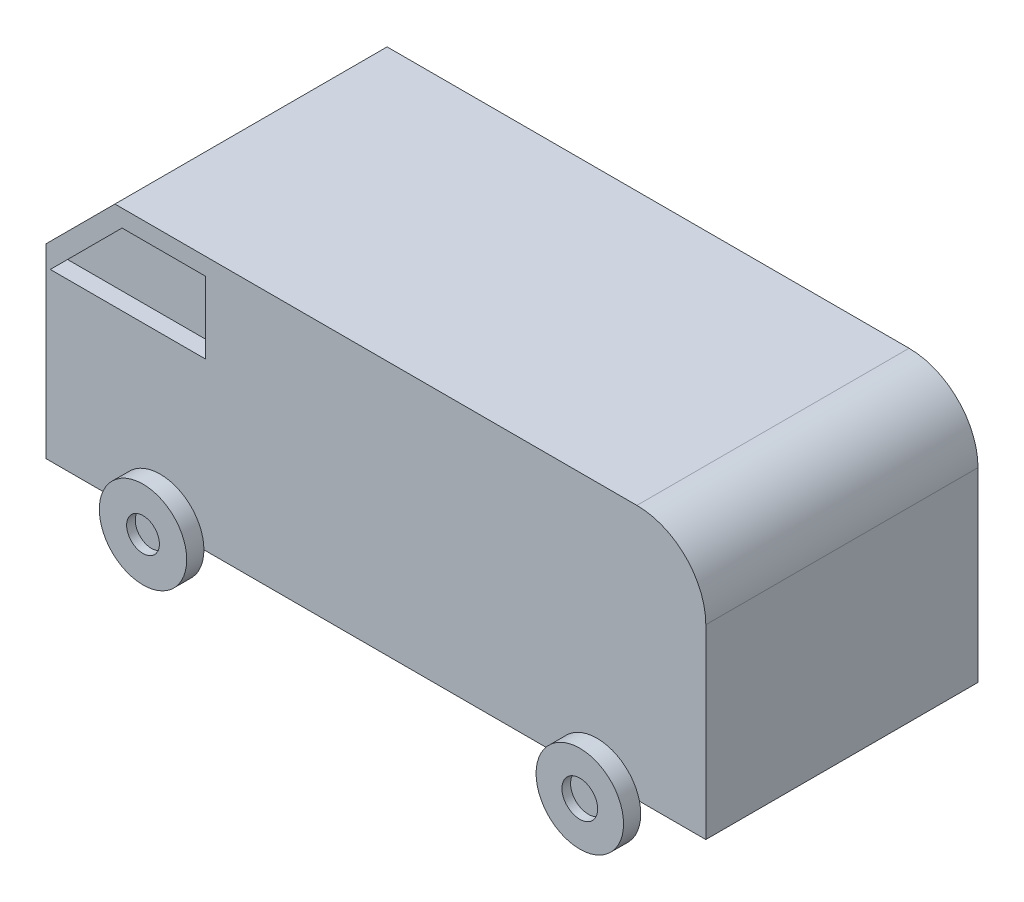
SolidWorks part; units mm, degrees
ref_plane "Front Plane" through (0, 0, 0) normal (0, 0, 1) x (1, 0, 0)
ref_plane "Top Plane" through (0, 0, 0) normal (0, 1, 0) x (1, 0, 0)
ref_plane "Right Plane" through (0, 0, 0) normal (1, 0, 0) x (0, 0, -1)
sketch "Sketch1" plane through (0, 0, 0) normal (0, 1, 0) x (1, 0, 0)
  line L1 (-191.5, -79) -> (191.5, -79)
  line L2 (-191.5, -79) -> (-191.5, 79)
  line L3 (-191.5, 79) -> (191.5, 79)
  line L4 (191.5, -79) -> (191.5, 79)
  line L5 (-191.5, -79) -> (191.5, 79) construction
  line L6 (-191.5, 79) -> (191.5, -79) construction
  point P0 (0, 0)
  dimension "D1" = 383
  dimension "D2" = 158
extrude "Boss-Extrude1" add sketch "Sketch1" along normal blind 148
chamfer "Chamfer1" distance 40 1 edges at (-191.5, 148, 0)
fillet "Fillet2" radius 40 1 edges at (191.5, 148, 0)
sketch "Sketch2" plane through (0, 0, 79) normal (0, 0, 1) x (1, 0, 0)
  line L5 (-147.3579, 138) -> (-188.9979, 96.36)
  line L6 (-188.9979, 96.36) -> (-98.9979, 96.36)
  line L7 (-98.9979, 96.36) -> (-98.9979, 138)
  line L8 (-98.9979, 138) -> (-147.3579, 138)
  line L9 (-151.5, 148) -> (151.5, 148) construction
  line L10 (-151.5, 148) -> (-191.5, 108) construction
  line L11 (-98.9979, 138) -> (-98.9979, 96.36)
  line L12 (-188.9979, 96.36) -> (-147.3579, 138)
  line L13 (-98.9979, 138) -> (-147.3579, 138)
  line L14 (-188.9979, 96.36) -> (-98.9979, 96.36)
  line L15 (-98.9979, 96.36) -> (-98.9979, 138)
  dimension "D1" = 90
  dimension "D2" = 41.64
  dimension "D3" = 10
  dimension "D4" = 10
extrude "Cut-Extrude1" cut sketch "Sketch2" against normal blind 10 contours L7 L8 L5 L6
sketch "Sketch3" plane through (0, 0, 79) normal (0, 0, 1) x (1, 0, 0)
  line L0 (-191.5, 0) -> (191.5, 0) construction
  circle A0 centre (-125.1901, 0) radius 25.359
  circle A1 centre (121.1382, 0) radius 0.0789
  circle A3 centre (128.3591, -6.0177) radius 25.3835
  point P9 (0, 0)
extrude "Boss-Extrude2" add sketch "Sketch3" along normal blind 10
sketch "Sketch4" plane through (0, 0, -79) normal (0, 0, -1) x (-1, 0, 0)
  line L0 (-191.5, 0) -> (191.5, 0) construction
  circle A0 centre (-132.5428, 0) radius 25.3796
  circle A1 centre (116.2821, 0) radius 25.1402
extrude "Boss-Extrude3" add sketch "Sketch4" along normal blind 10
sketch "Sketch5" plane through (-191.5, 0, 0) normal (-1, 0, 0) x (0, 0, 1)
  circle A0 centre (-53.7195, 34.6705) radius 14.3228
  circle A1 centre (30.2804, 34.6705) radius 16.2324
extrude "Boss-Extrude4" add sketch "Sketch5" along normal blind 10
sketch "Sketch6" plane through (0, 0, 89) normal (0, 0, 1) x (1, 0, 0)
  circle A0 centre (-125.1901, 0) radius 9.5203
  circle A1 centre (128.3591, -6.0177) radius 10.3671
extrude "Cut-Extrude3" cut sketch "Sketch6" against normal blind 5
